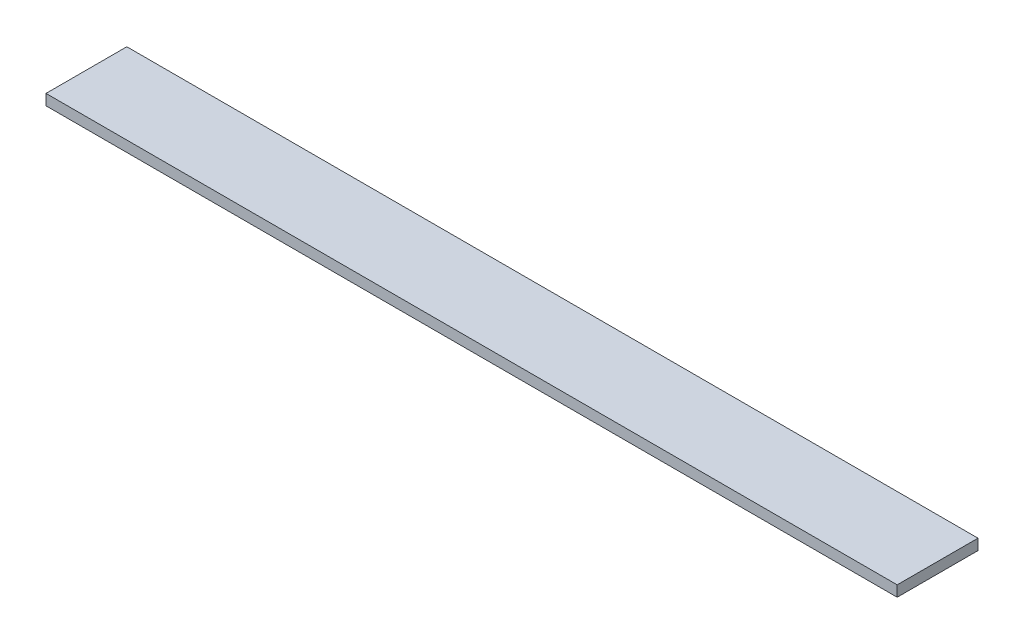
SolidWorks part; units mm, degrees
ref_plane "Спереди" through (0, 0, 0) normal (0, 0, 1) x (1, 0, 0)
ref_plane "Сверху" through (0, 0, 0) normal (0, 1, 0) x (1, 0, 0)
ref_plane "Справа" through (0, 0, 0) normal (1, 0, 0) x (0, 0, -1)
sketch "Эскиз1" plane through (0, 0, 0) normal (1, 0, 0) x (0, 0, -1)
  line L1 (-15, -2) -> (15, -2)
  line L2 (-15, -2) -> (-15, 2)
  line L3 (-15, 2) -> (15, 2)
  line L4 (15, -2) -> (15, 2)
  line L5 (-15, -2) -> (15, 2) construction
  line L6 (-15, 2) -> (15, -2) construction
  point P0 (0, 0)
  dimension "D1" = 4
  dimension "D2" = 30
extrude "Бобышка-Вытянуть1" add sketch "Эскиз1" along normal blind 316
